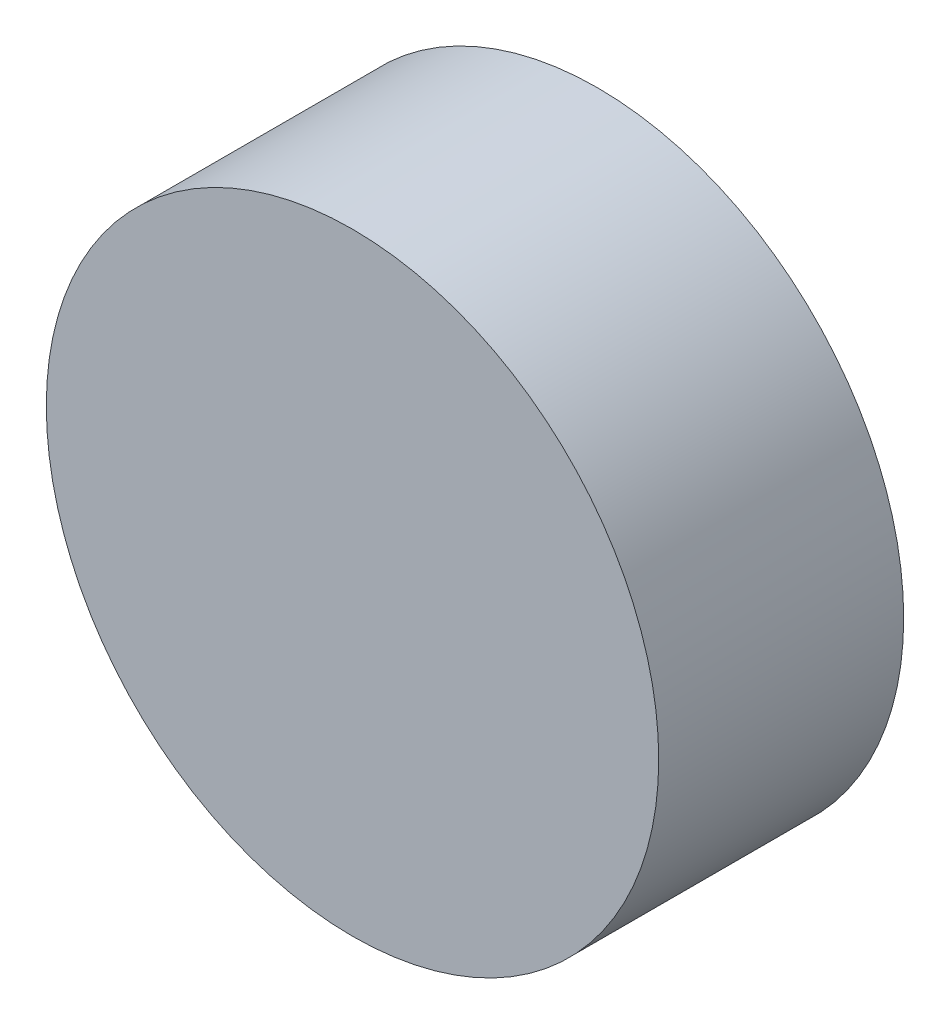
SolidWorks part; units mm, degrees
ref_plane "Alzado" through (0, 0, 0) normal (0, 0, 1) x (1, 0, 0)
ref_plane "Planta" through (0, 0, 0) normal (0, 1, 0) x (1, 0, 0)
ref_plane "Vista lateral" through (0, 0, 0) normal (1, 0, 0) x (0, 0, -1)
sketch "Croquis1" plane through (0, 0, 0) normal (0, 0, 1) x (1, 0, 0)
  circle A0 centre (0, 0) radius 2.5
  dimension "D1" = 5
extrude "Saliente-Extruir1" add sketch "Croquis1" along normal blind 2
